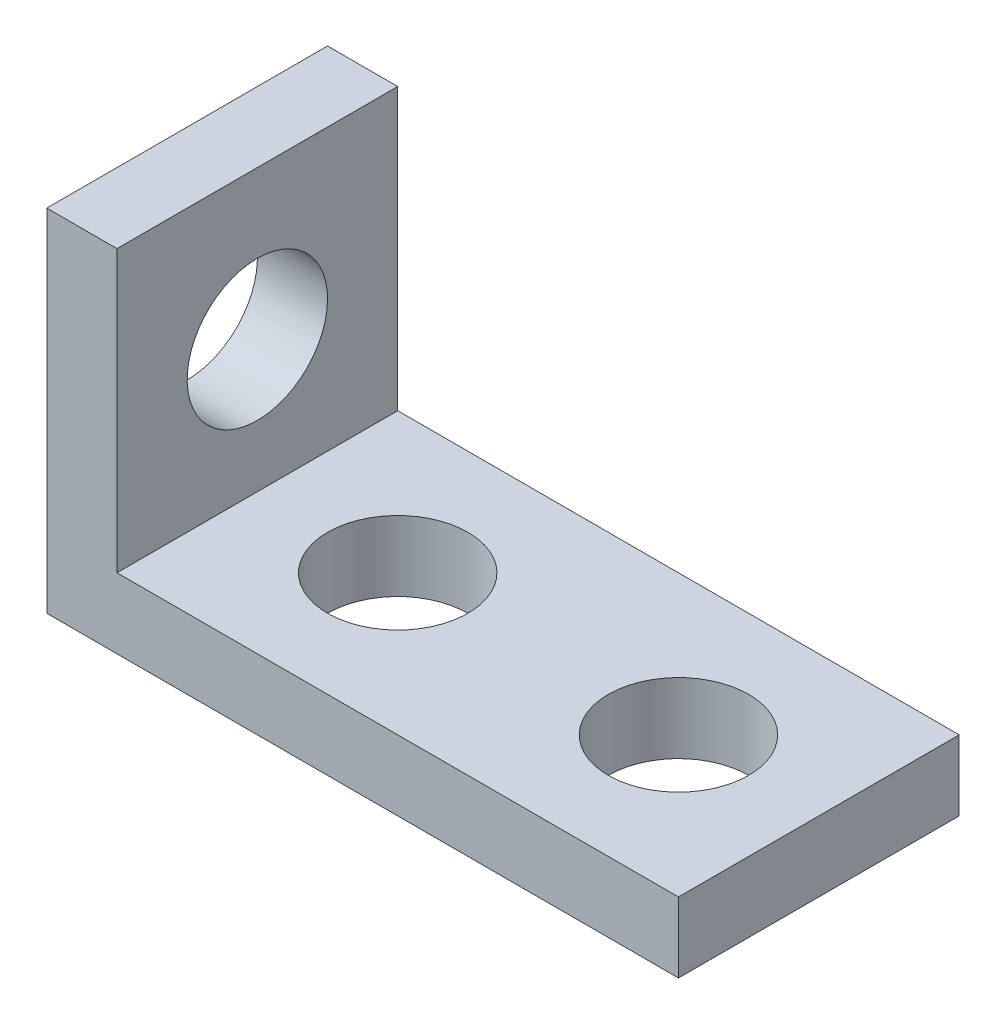
SolidWorks part; units mm, degrees
ref_plane "Front Plane" through (0, 0, 0) normal (0, 0, 1) x (1, 0, 0)
ref_plane "Top Plane" through (0, 0, 0) normal (0, 1, 0) x (1, 0, 0)
ref_plane "Right Plane" through (0, 0, 0) normal (1, 0, 0) x (0, 0, -1)
sketch "Sketch1" plane through (0, 0, 0) normal (0, 0, 1) x (1, 0, 0)
  line L0 (0, 0) -> (0, 15.875)
  line L1 (0, 15.875) -> (3.175, 15.875)
  line L2 (3.175, 15.875) -> (3.175, 3.175)
  line L3 (3.175, 3.175) -> (28.575, 3.175)
  line L4 (28.575, 3.175) -> (28.575, 0)
  line L5 (28.575, 0) -> (0, 0)
  dimension "D1" = 3.175
  dimension "D2" = 3.175
  dimension "D3" = 15.875
  dimension "D4" = 28.575
extrude "Boss-Extrude1" add sketch "Sketch1" along normal blind 12.7
sketch "Sketch2" plane through (0, 3.175, 0) normal (0, 1, 0) x (1, 0, 0)
  line L0 (3.175, -6.35) -> (28.575, -6.35) construction
  line L1 (3.175, -12.7) -> (3.175, 0) construction
  line L2 (28.575, -12.7) -> (28.575, 0) construction
  circle A0 centre (9.525, -6.35) radius 3.175
  circle A1 centre (22.225, -6.35) radius 3.175
  dimension "D1" = 6.35
  dimension "D2" = 12.7
  dimension "D3" = 6.35
extrude "Cut-Extrude1" cut sketch "Sketch2" against normal through all
sketch "Sketch3" plane through (3.175, 0, 0) normal (1, 0, 0) x (0, 0, -1)
  line L0 (-6.35, 15.875) -> (-6.35, 3.175) construction
  line L1 (-12.7, 15.875) -> (0, 15.875) construction
  line L2 (-12.7, 3.175) -> (0, 3.175) construction
  line L3 (-12.7, 0) -> (0, 0) construction
  circle A0 centre (-6.35, 9.144) radius 3.175
  dimension "D1" = 6.35
  dimension "D2" = 9.144
extrude "Cut-Extrude2" cut sketch "Sketch3" against normal through all
